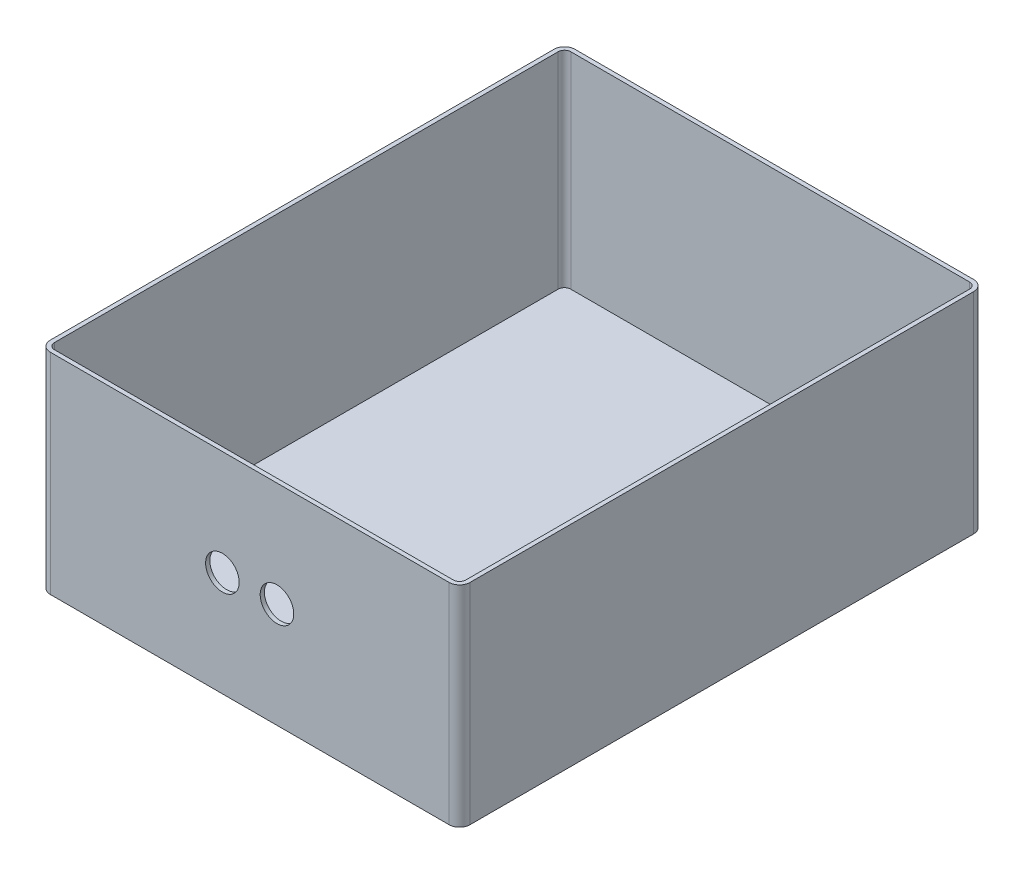
SolidWorks part; units mm, degrees
ref_plane "Front Plane" through (0, 0, 0) normal (0, 0, 1) x (1, 0, 0)
ref_plane "Top Plane" through (0, 0, 0) normal (0, 1, 0) x (1, 0, 0)
ref_plane "Right Plane" through (0, 0, 0) normal (1, 0, 0) x (0, 0, -1)
sketch "Sketch3" plane through (0, 0, 0) normal (0, 1, 0) x (1, 0, 0)
  line L0 (89.4029, 224.2043) -> (-5.5971, 224.2043)
  line L1 (-10.5971, 224.2043) -> (189.4029, 224.2043)
  line L2 (-10.5971, 224.2043) -> (-10.5971, -25.7957)
  line L3 (-10.5971, -25.7957) -> (189.4029, -25.7957)
  line L4 (189.4029, 224.2043) -> (189.4029, -25.7957)
  line L5 (89.4029, -25.7957) -> (184.4029, -25.7957)
  line L6 (189.4029, -25.7957) -> (189.4029, 219.2043)
  line L7 (-10.5971, 224.2043) -> (-10.5971, -20.7957)
  arc A0 (-5.5971, 224.2043) -> (-10.5971, 219.2043) centre (-5.5971, 219.2043) ccw
  arc A1 (189.4029, 219.2043) -> (184.4029, 224.2043) centre (184.4029, 219.2043) ccw
  arc A2 (-10.5971, -20.7957) -> (-5.5971, -25.7957) centre (-5.5971, -20.7957) ccw
  arc A3 (184.4029, -25.7957) -> (189.4029, -20.7957) centre (184.4029, -20.7957) ccw
extrude "Boss-Extrude2" add sketch "Sketch3" along normal blind 100 contours L3 A3 L4 A1 L1 L0 A0 L7 A2
shell "Shell2" thickness 2
sketch "Sketch5" plane through (0, 0, 25.7957) normal (0, 0, 1) x (1, 0, 0)
  line L0 (-5.5971, 100) -> (89.4029, 100)
  line L1 (-5.5971, 100) -> (184.4029, 100) construction
  line L2 (89.4029, 100) -> (89.4029, 0)
  line L3 (-5.5971, 0) -> (184.4029, 0) construction
  line L4 (89.4029, 50) -> (102.4029, 50)
  line L5 (89.4029, 50) -> (76.4029, 50)
  circle A0 centre (76.4029, 50) radius 8
  circle A1 centre (102.4029, 50) radius 8
extrude "Cut-Extrude1" cut sketch "Sketch5" against normal blind 100
